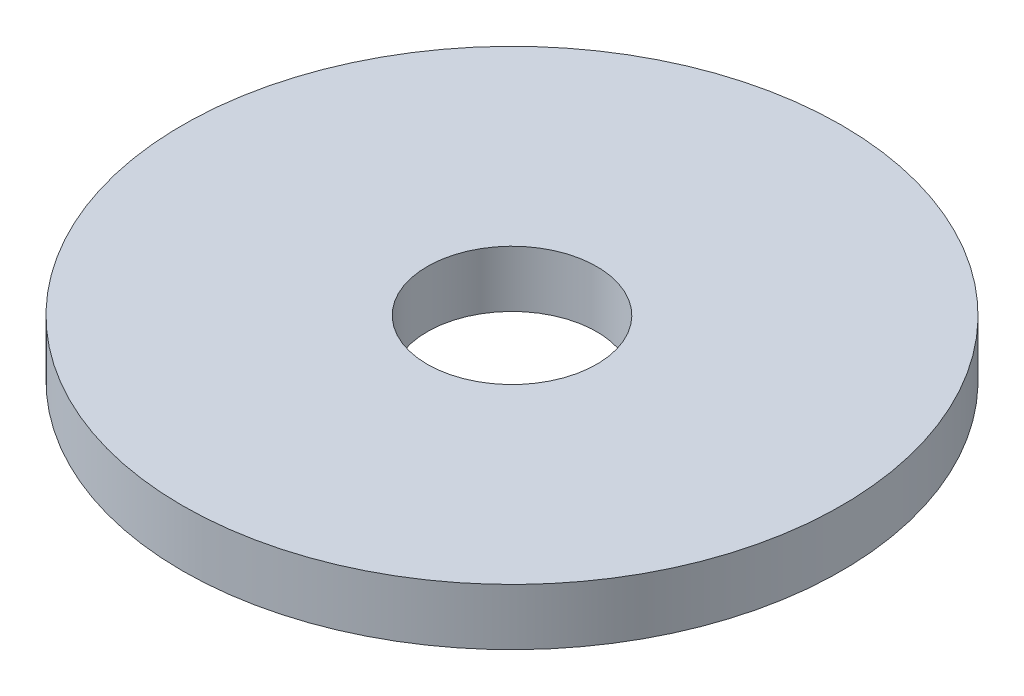
SolidWorks part; units mm, degrees
ref_plane "Front Plane" through (0, 0, 0) normal (0, 0, 1) x (1, 0, 0)
ref_plane "Top Plane" through (0, 0, 0) normal (0, 1, 0) x (1, 0, 0)
ref_plane "Right Plane" through (0, 0, 0) normal (1, 0, 0) x (0, 0, -1)
sketch "Sketch1" plane through (0, 0, 0) normal (0, 0, 1) x (1, 0, 0)
  line L0 (0, 2.9683) -> (0, 0) construction
  line L1 (0, 0) -> (-17.5, 0) construction
  line L3 (-17.5, 0) -> (-4.5, 0)
  line L4 (-17.5, 0) -> (-17.5, -3)
  line L5 (-17.5, -3) -> (-4.5, -3)
  line L6 (-4.5, 0) -> (-4.5, -3)
  dimension "D1" = 4.5
  dimension "D2" = 17.5
  dimension "D3" = 3
revolve "Revolve1" add sketch "Sketch1" angle 360 about L0
